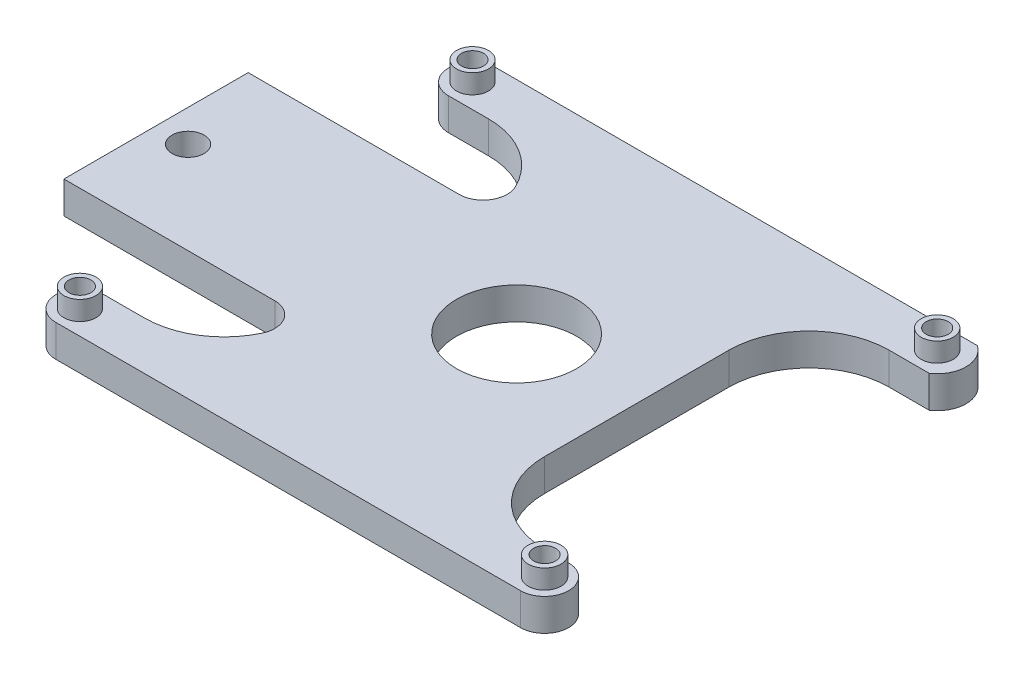
SolidWorks part; units mm, degrees
ref_plane "Front Plane" through (0, 0, 0) normal (0, 0, 1) x (1, 0, 0)
ref_plane "Top Plane" through (0, 0, 0) normal (0, 1, 0) x (1, 0, 0)
ref_plane "Right Plane" through (0, 0, 0) normal (1, 0, 0) x (0, 0, -1)
sketch "Sketch2" plane through (0, 0, 0) normal (0, 1, 0) x (1, 0, 0)
  line L0 (-16.7596, 39.5587) -> (41.2404, 39.5587) construction
  line L1 (-16.7596, 42.5587) -> (44.2404, 42.5587)
  line L3 (-19.7596, -12.4413) -> (41.2404, -12.4413)
  line L5 (-16.7596, 42.5587) -> (41.2404, 43.1643)
  line L6 (-16.7596, 36.5587) -> (-11.7596, 36.5587)
  line L7 (-16.7596, -9.4413) -> (41.2404, -9.4413) construction
  line L8 (-16.7596, -6.4413) -> (-11.7596, -6.4413)
  line L9 (-16.7596, -12.4413) -> (41.2404, -12.4413)
  line L10 (38.2404, 36.5587) -> (43.2404, 36.5587)
  line L14 (28.2404, 26.5587) -> (28.2404, 3.5587)
  line L15 (38.2404, -6.4413) -> (41.2404, -6.4413)
  line L16 (-31.7596, 23.5587) -> (-31.7596, 26.5587)
  line L17 (-5.4351, 26.5587) -> (-28.7596, 26.5587)
  line L19 (-5.4351, 3.5587) -> (-28.7596, 3.5587)
  line L20 (-31.7596, 23.5587) -> (-31.7596, 6.5587)
  line L21 (-31.7596, 26.5587) -> (-28.7596, 26.5587)
  line L22 (-31.7596, 6.5587) -> (-31.7596, 3.5587)
  line L23 (-31.7596, 3.5587) -> (-28.7596, 3.5587)
  circle A0 centre (-16.7596, 39.5587) radius 1.375
  circle A1 centre (41.2404, 39.5587) radius 1.375
  circle A2 centre (41.2404, -9.4413) radius 1.375
  circle A3 centre (-16.7596, -9.4413) radius 1.375
  arc A4 (-16.7596, 42.5587) -> (-16.7596, 36.5587) centre (-16.7596, 39.5587) ccw
  arc A5 (43.2404, 36.5587) -> (41.2404, 43.1643) centre (41.2404, 39.5587) ccw
  arc A6 (-16.7596, -6.4413) -> (-16.7596, -12.4413) centre (-16.7596, -9.4413) ccw
  arc A7 (41.2404, -12.4413) -> (41.2404, -6.4413) centre (41.2404, -9.4413) ccw
  circle A8 centre (13.2404, 15.0587) radius 7.5
  arc A9 (-11.7596, -6.4413) -> (-2.7246, -0.727) centre (-11.7596, 3.5587) ccw
  arc A10 (28.2404, 3.5587) -> (38.2404, -6.4413) centre (38.2404, 3.5587) ccw
  arc A11 (28.2404, 26.5587) -> (38.2404, 36.5587) centre (38.2404, 26.5587) cw
  arc A12 (-2.7246, 30.8445) -> (-11.7596, 36.5587) centre (-11.7596, 26.5587) ccw
  arc A15 (-2.7246, -0.727) -> (-5.4351, 3.5587) centre (-5.4351, 0.5587) ccw
  arc A16 (-2.7246, 30.8445) -> (-5.4351, 26.5587) centre (-5.4351, 29.5587) cw
  point P12 (12.2404, 39.5587)
  point P17 (12.2404, -9.4413)
  point P30 (28.2404, -6.4413)
  point P41 (-31.7596, 26.5587)
  point P46 (-1.7596, 26.5587)
  dimension "D1" = 2.75
  dimension "D2" = 2.75
  dimension "D15" = 6
  dimension "D13" = 15
  dimension "D16" = 10
  dimension "D3" = 58
  dimension "D4" = 49
  dimension "D6" = 23
  dimension "D7" = 15
  dimension "D8" = 3
  dimension "D9" = 3
  dimension "D10" = 3
  dimension "D11" = 15
  dimension "D12" = 24.5
  dimension "D14" = 58
  dimension "D17" = 30
extrude "Boss-Extrude1" add sketch "Sketch2" along normal blind 4 contours A12 L17 L20 L19 A9 L8 A6 L3 A7 L15 A10 L14 A11 L10 A5 L1 A4 L6 A8 A3 A2 A1 A0
sketch "Sketch3" plane through (0, 4, 0) normal (0, 1, 0) x (1, 0, 0)
  line L0 (-5.4351, 26.5587) -> (-31.7596, 26.5587) construction
  line L1 (-31.7596, 3.5587) -> (-5.4351, 3.5587) construction
  line L2 (-31.7596, 3.5587) -> (-31.7596, 26.5587) construction
  circle A0 centre (-27.7596, 15.0587) radius 2
  dimension "D1" = 11.5
  dimension "D2" = 11.5
  dimension "D3" = 4
extrude "Cut-Extrude1" cut sketch "Sketch3" against normal blind 10
sketch "Sketch7" plane through (0, 4, 0) normal (0, 1, 0) x (1, 0, 0)
  circle A0 centre (-16.7596, 39.5587) radius 1.9951
  circle A1 centre (-16.7596, 39.5587) radius 1.375
  circle A2 centre (-16.7596, -9.4413) radius 1.375
  circle A3 centre (-16.7596, -9.4413) radius 2.0019
  circle A4 centre (41.2404, -9.4413) radius 1.375
  circle A5 centre (41.2404, -9.4413) radius 2.0502
  circle A6 centre (41.2404, 39.5587) radius 1.375
  circle A7 centre (41.2404, 39.5587) radius 2.0023
extrude "Boss-Extrude2" add sketch "Sketch7" along normal blind 2.4
